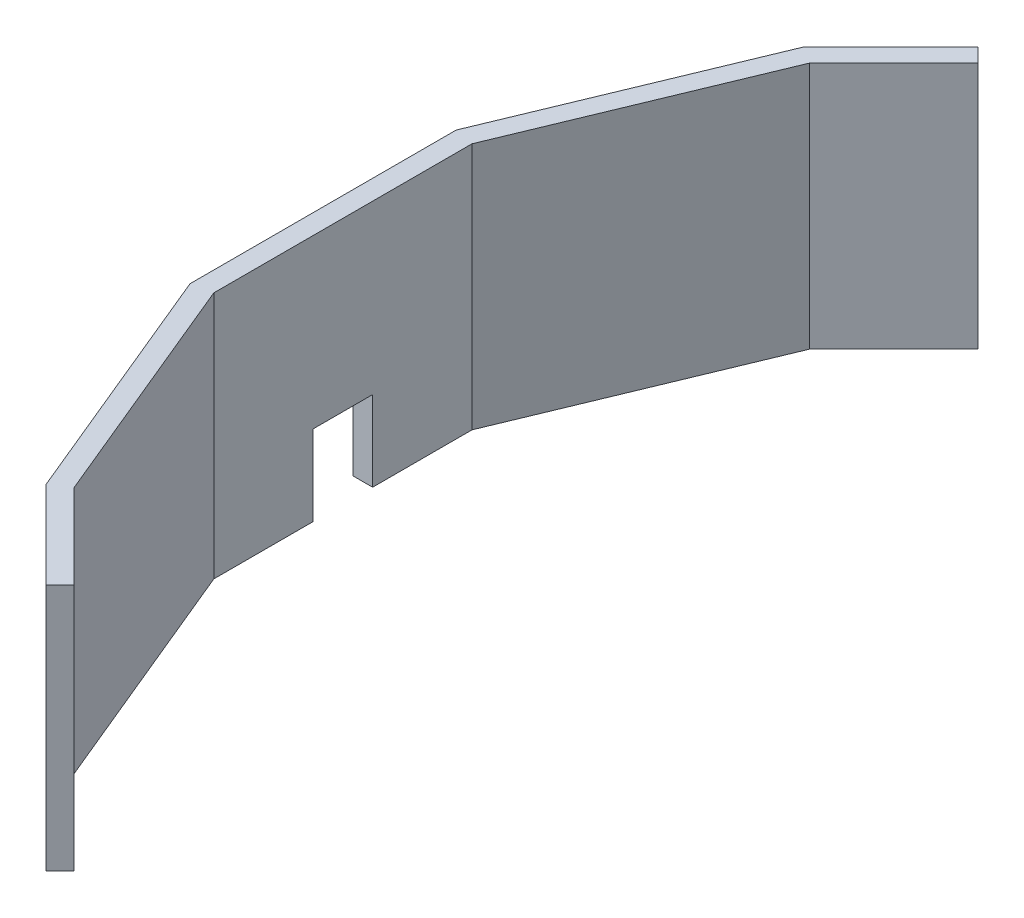
SolidWorks part; units mm, degrees
material "Acrylic (Medium-high impact)"
ref_plane "Front Plane" through (0, 0, 0) normal (0, 0, 1) x (1, 0, 0)
ref_plane "Top Plane" through (0, 0, 0) normal (0, 1, 0) x (1, 0, 0)
ref_plane "Right Plane" through (0, 0, 0) normal (1, 0, 0) x (0, 0, -1)
sketch "Sketch2" plane through (0, 0, 0) normal (0, 1, 0) x (1, 0, 0)
  line L0 (0, 0) -> (-655, 0) construction
  line L1 (0, 0) -> (-605.1411, 250.6576) construction
  line L2 (0, 0) -> (-463.1549, 463.1549) construction
  line L3 (0, 0) -> (-605.1411, -250.6576) construction
  line L4 (0, 0) -> (-463.1549, -463.1549) construction
  line L5 (-555.2822, -371.0277) -> (-371.0277, -555.2822)
  line L6 (-655, 130.2876) -> (-655, -130.2876)
  line L7 (-655, -130.2876) -> (-555.2822, -371.0277)
  line L8 (-555.2822, 371.0277) -> (-655, 130.2876)
  line L9 (-660.5957, 265.7142) -> (-655, 271.3099)
  line L10 (-555.2822, 371.0277) -> (-265.7142, 660.5957)
  line L11 (-572.2374, -382.3568) -> (-385.1698, -569.4243)
  line L12 (-675, -134.2658) -> (-572.2374, -382.3568)
  line L13 (-675, 134.2658) -> (-675, -134.2658)
  line L14 (-572.2374, 382.3568) -> (-675, 134.2658)
  line L15 (-572.2374, 382.3568) -> (-279.8564, 674.7378)
  line L16 (-463.1549, 463.1549) -> (-477.2971, 477.2971)
  line L17 (-463.1549, -463.1549) -> (-477.2971, -477.2971)
  line L18 (-470.226, -456.0839) -> (-484.3681, -470.226)
  line L19 (-484.3681, 470.226) -> (-470.226, 456.0839)
  point P10 (-463.1549, -463.1549)
  point P14 (-655, 0)
  point P17 (-605.1411, -250.6576)
  point P20 (-605.1411, 250.6576)
  point P23 (-463.1549, 463.1549)
  dimension "D1" = 20
  dimension "D2" = 22.5
  dimension "D3" = 22.5
  dimension "D4" = 22.5
  dimension "D5" = 22.5
  dimension "D6" = 10
  dimension "D7" = 10
extrude "Boss-Extrude1" add sketch "Sketch2" along normal blind 250
sketch "Sketch3" plane through (-655, 0, 0) normal (1, 0, 0) x (0, 0, -1)
  line L1 (-30, -81) -> (30, -81)
  line L2 (-30, -81) -> (-30, 81)
  line L3 (-30, 81) -> (30, 81)
  line L4 (30, -81) -> (30, 81)
  line L5 (-30, -81) -> (30, 81) construction
  line L6 (-30, 81) -> (30, -81) construction
  point P0 (0, 0)
  dimension "D1" = 162
  dimension "D2" = 60
extrude "Cut-Extrude1" cut sketch "Sketch3" against normal blind 20
